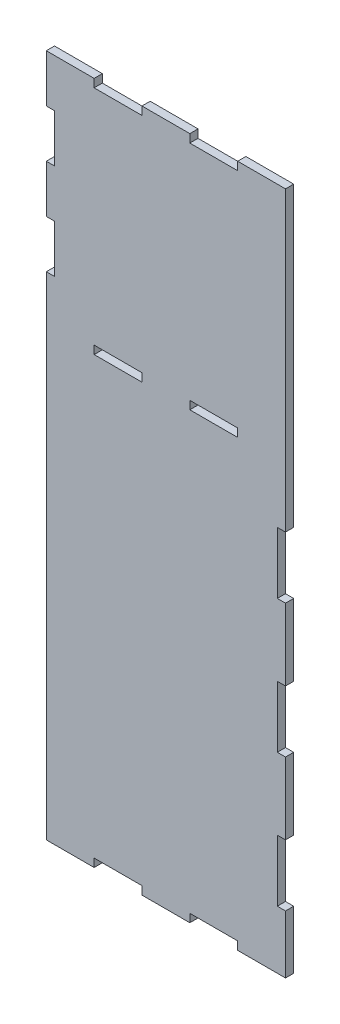
SolidWorks part; units mm, degrees
material "Maple"
ref_plane "Front Plane" through (0, 0, 0) normal (0, 0, 1) x (1, 0, 0)
ref_plane "Top Plane" through (0, 0, 0) normal (0, 1, 0) x (1, 0, 0)
ref_plane "Right Plane" through (0, 0, 0) normal (1, 0, 0) x (0, 0, -1)
sketch "Sketch1" plane through (0, 0, 0) normal (0, 0, 1) x (1, 0, 0)
  line L0 (280, 1000) -> (350, 1000)
  line L1 (0, 0) -> (70, 0)
  line L3 (0, 1000) -> (70, 1000)
  line L5 (0, 1000) -> (70, 1000)
  line L8 (70, 1000) -> (70, 988)
  line L9 (210, 1000) -> (210, 988)
  line L10 (0, 1000) -> (0, 930)
  line L11 (350, 1000) -> (350, 565)
  line L12 (140, 988) -> (140, 1000)
  line L13 (280, 988) -> (280, 1000)
  line L14 (140, 1000) -> (210, 1000)
  line L15 (0, 650) -> (350, 650) construction
  line L16 (0, 325) -> (338, 325) construction
  line L17 (350, 1000) -> (350, 988) [skipped]
  line L18 (280, 988) -> (210, 988)
  line L19 (140, 988) -> (70, 988)
  line L20 (280, 0) -> (350, 0)
  line L23 (70, 662) -> (70, 650)
  line L24 (210, 662) -> (210, 650)
  line L25 (140, 650) -> (140, 662)
  line L26 (280, 650) -> (280, 662)
  line L28 (280, 650) -> (210, 650)
  line L29 (140, 650) -> (70, 650)
  line L30 (70, 662) -> (140, 662)
  line L31 (210, 662) -> (280, 662)
  line L33 (0, 662) -> (70, 662) [skipped]
  line L34 (0, 662) -> (70, 662) [skipped]
  line L35 (140, 662) -> (210, 662) [skipped]
  line L36 (280, 662) -> (350, 662) [skipped]
  line L37 (70, 12) -> (70, 0)
  line L38 (210, 12) -> (210, 0)
  line L39 (140, 0) -> (140, 12)
  line L40 (280, 0) -> (280, 12)
  line L41 (140, 0) -> (210, 0)
  line L42 (70, 12) -> (140, 12)
  line L43 (210, 12) -> (280, 12)
  line L44 (280, 12) -> (350, 12) [skipped]
  line L45 (280, 0) -> (210, 0) [skipped]
  line L46 (140, 12) -> (210, 12) [skipped]
  line L47 (140, 0) -> (70, 0) [skipped]
  line L48 (0, 12) -> (70, 12) [skipped]
  line L49 (0, 12) -> (70, 12) [skipped]
  line L50 (350, 85) -> (350, 0)
  line L51 (350, 370) -> (338, 370)
  line L53 (350, 280) -> (338, 280)
  line L54 (338, 370) -> (338, 280)
  line L55 (350, 565) -> (338, 565)
  line L57 (350, 475) -> (338, 475)
  line L58 (338, 565) -> (338, 475)
  line L59 (350, 175) -> (338, 175)
  line L61 (350, 85) -> (338, 85)
  line L62 (338, 175) -> (338, 85)
  line L63 (350, 280) -> (350, 175)
  line L64 (350, 475) -> (350, 370)
  line L65 (0, 860) -> (0, 790)
  line L66 (0, 930) -> (12, 930)
  line L68 (0, 860) -> (12, 860)
  line L69 (12, 930) -> (12, 860)
  line L70 (0, 790) -> (12, 790)
  line L72 (0, 720) -> (12, 720)
  line L73 (12, 790) -> (12, 720)
  line L74 (0, 720) -> (0, 0)
  point P67 (338, 325)
  point P68 (344, 475)
  point P77 (0, 0)
  point P78 (0, 0)
  point P79 (0, 0)
  dimension "D1" = 350
  dimension "D2" = 1000
  dimension "D3" = 70
  dimension "D4" = 12
  dimension "D6" = 2
  dimension "D7" = 70
  dimension "D8" = 70
  dimension "D9" = 70
  dimension "D10" = 70
  dimension "D11" = 70
  dimension "D12" = 12
  dimension "D13" = 12
  dimension "D15" = 338
  dimension "D16" = 350
  dimension "D17" = 325
  dimension "D18" = 90
  dimension "D19" = 90
  dimension "D20" = 90
  dimension "D21" = 105
  dimension "D22" = 105
  dimension "D23" = 12
  dimension "D24" = 70
  dimension "D25" = 70
  dimension "D26" = 70
  dimension "D27" = 70
  dimension "D28" = 12
  dimension "D5" = 3
  dimension "D14" = 2
extrude "Boss-Extrude2" add sketch "Sketch1" along normal blind 12 contours L64 L57 L58 L55 L11 L0 L13 L18 L9 L14 L12 L19 L8 L3 L10 L1 L37 L42 L39 L41 L38 L43 L40 L20 L50 L61 L62 L59 L63 L53 L54 L51 L23 L30 L25 L29 L24 L31 L26 L28
